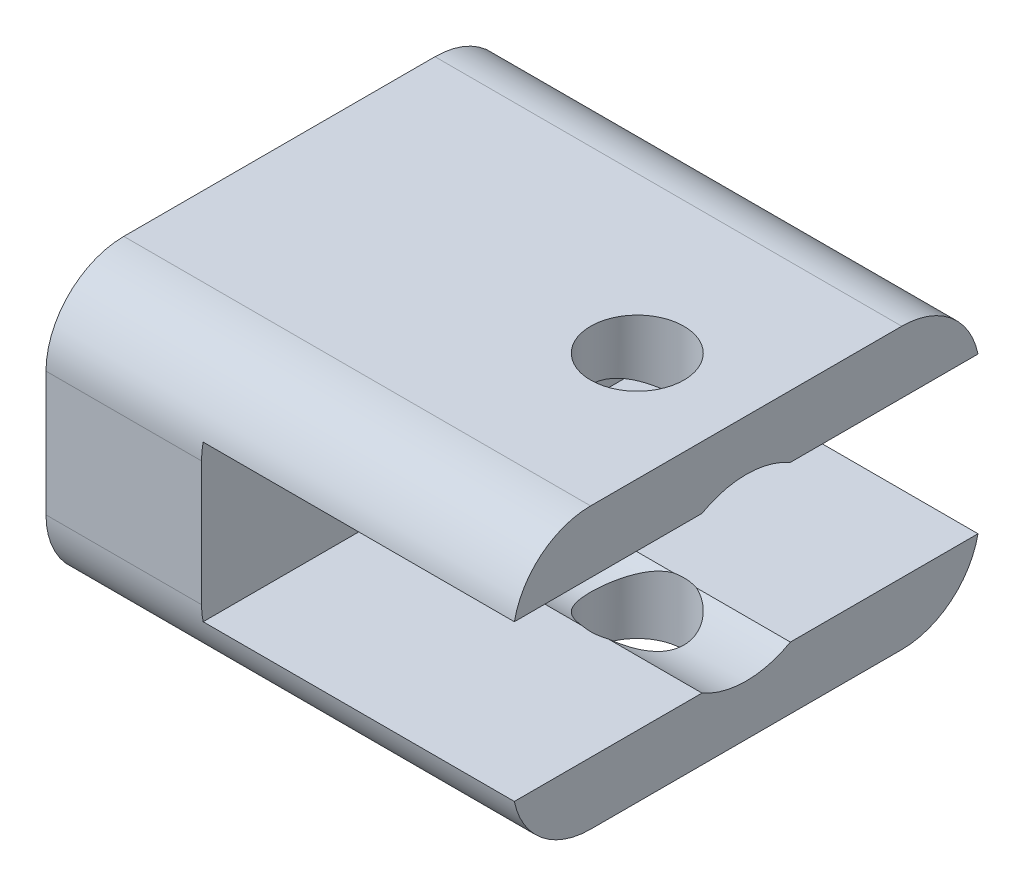
SolidWorks part; units mm, degrees
ref_plane "Plan de face" through (0, 0, 0) normal (0, 0, 1) x (1, 0, 0)
ref_plane "Plan de dessus" through (0, 0, 0) normal (0, 1, 0) x (1, 0, 0)
ref_plane "Plan de droite" through (0, 0, 0) normal (1, 0, 0) x (0, 0, -1)
ref_plane "Plan1" through (0, 0, 0) normal (0, -1, 0) x (1, 0, 0)
sketch "Esquisse1" plane through (0, 0, 0) normal (0, -1, 0) x (1, 0, 0)
  line L0 (0, 30) -> (0, 0)
  line L1 (0, 0) -> (30, 0)
  line L2 (30, 0) -> (30, 30)
  line L3 (30, 30) -> (0, 30)
extrude "Boss.-Extru.1" add sketch "Esquisse1" against normal blind 4
ref_plane "Plan2" through (22.4, 0, 0) normal (1, 0, 0) x (0, 0, -1)
sketch "Esquisse2" plane through (22.4, 0, 0) normal (1, 0, 0) x (0, 0, -1)
  line L0 (-12.0606, 4) -> (-17.9394, 4)
  arc A0 (-17.9394, 4) -> (-12.0606, 4) centre (-15, 9) ccw
extrude "Enlèv. mat.-Extru.1" cut sketch "Esquisse2" against normal blind 12.4
sketch "Esquisse3" plane through (0, 4, 0) normal (0, 1, 0) x (-1, 0, 0)
  line L0 (-10, 30) -> (0, 30)
  line L1 (0, 30) -> (0, 0)
  line L2 (0, 0) -> (-10, 0)
  line L3 (-10, 0) -> (-10, 30)
extrude "Boss.-Extru.2" add sketch "Esquisse3" along normal blind 14
sketch "Esquisse4" plane through (10, 0, 0) normal (1, 0, 0) x (0, 0, -1)
  line L0 (0, 14) -> (-30, 14)
  line L1 (-30, 14) -> (-30, 18)
  line L2 (-30, 18) -> (0, 18)
  line L3 (0, 18) -> (0, 14)
extrude "Boss.-Extru.3" add sketch "Esquisse4" along normal blind 20
sketch "Esquisse5" plane through (30, 0, 0) normal (1, 0, 0) x (0, 0, -1)
  line L0 (0, 18) -> (-30, 18) construction
  line L1 (-30, 4) -> (-30, 0) construction
  circle A1 centre (-15, 9) radius 5.75
  dimension "D1" = 11.5
  dimension "D2" = 9
  dimension "D3" = 15
extrude "Enlèv. mat.-Extru.2" cut sketch "Esquisse5" against normal blind 20
ref_plane "Plan3" through (0, 0, 15) normal (0, 0, -1) x (-1, 0, 0)
sketch "Esquisse7" plane through (0, 0, 15) normal (0, 0, -1) x (-1, 0, 0)
  line L0 (-10, 14.75) -> (-10, 9)
  line L1 (-10, 9) -> (0, 9)
  line L2 (0, 9) -> (0, 11.75)
  line L3 (0, 11.75) -> (-7, 11.75)
  line L4 (-7, 11.75) -> (-10, 14.75)
  line L5 (-10, 9) -> (0, 9) construction
  line L6 (0, 0) -> (-30, 0) construction
  line L7 (0, 18) -> (0, 0) construction
  line L8 (-10, 14) -> (-10, 4) construction
  dimension "D1" = 2.75
  dimension "D2" = 9
  dimension "D3" = 7
  dimension "D4" = 45
revolve "Enlèvement de matière-Révolution1" cut sketch "Esquisse7" angle 360 about L5
hole_wizard "Diamètre du perçage Ø6.0 (6)1" positions "Esquisse9" profile "Esquisse8" hole size "Ø6.0" standard "Ansi Metric"
sketch "Esquisse9" plane through (0, 18, 0) normal (0, 1, 0) x (1, 0, 0)
  point P0 (23, -15)
sketch "Esquisse8" plane through (23, 18, 15) normal (1, 0, 0) x (0, 0, 1)
  line L0 (0, 0) -> (0, 3.25)
  line L1 (0, 3.25) -> (3, 3.25)
  line L2 (3, 3.25) -> (3, 0)
  line L5 (3, 0) -> (0, 0)
  line L11 (0, -6.35) -> (0, 107.95) construction
  dimension "Diamètre du perçage jusqu'au prochain" = 6
  dimension "Profondeur du perçage jusqu'au prochain" = 3.25
hole_wizard "Diamètre du perçage Ø6.0 (6)2" positions "Esquisse11" profile "Esquisse10" hole size "Ø6.0" standard "Ansi Metric"
sketch "Esquisse11" plane through (0, 0, 0) normal (0, -1, 0) x (-1, 0, 0)
  point P0 (-23, -15)
sketch "Esquisse10" plane through (23, 0, 15) normal (1, 0, 0) x (0, 0, -1)
  line L0 (0, 0) -> (0, 18)
  line L1 (0, 18) -> (3, 18)
  line L2 (3, 18) -> (3, 0)
  line L5 (3, 0) -> (0, 0)
  line L11 (0, -6.35) -> (0, 107.95) construction
  dimension "Diamètre du perçage jusqu'au prochain" = 6
  dimension "Profondeur du perçage jusqu'au prochain" = 18
fillet "Congé2" radius 5 4 edges at (15, 18, 0) (15, 0, 0) (15, 0, 30) (15, 18, 30)
